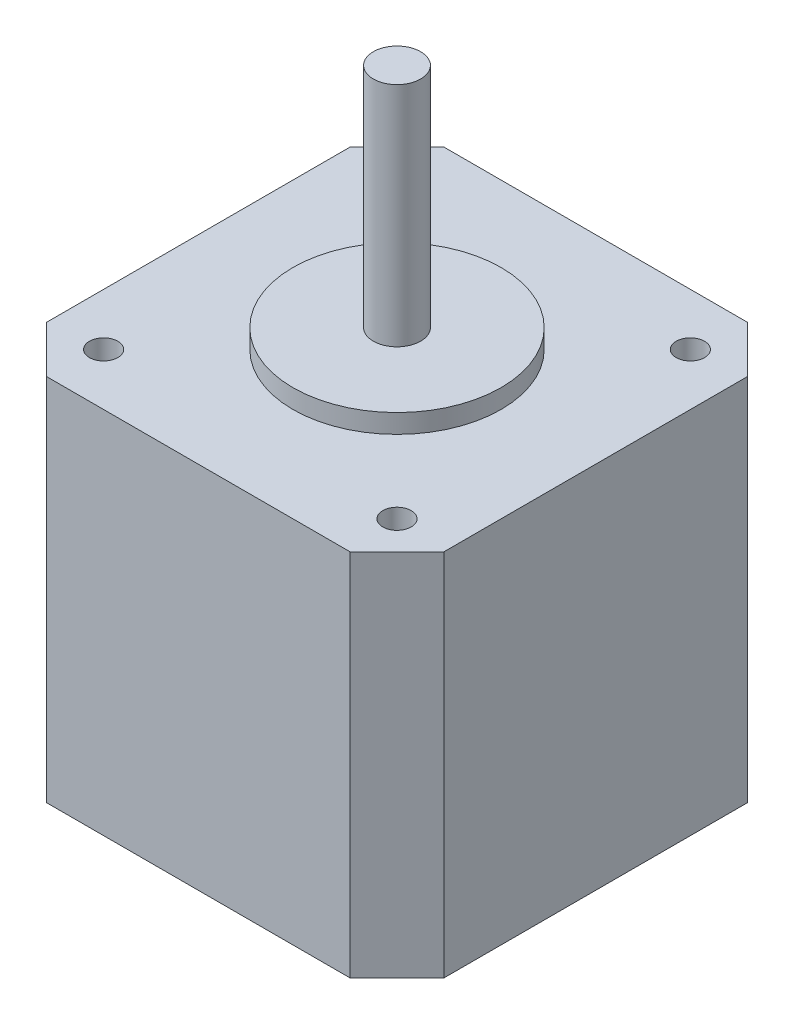
SolidWorks part; units mm, degrees
ref_plane "Front Plane" through (0, 0, 0) normal (0, 0, 1) x (1, 0, 0)
ref_plane "Top Plane" through (0, 0, 0) normal (0, 1, 0) x (1, 0, 0)
ref_plane "Right Plane" through (0, 0, 0) normal (1, 0, 0) x (0, 0, -1)
sketch "Sketch1" plane through (0, 0, 0) normal (0, 1, 0) x (1, 0, 0)
  line L1 (0, 0) -> (42, 0)
  line L2 (0, 0) -> (0, 42)
  line L3 (0, 42) -> (42, 42)
  line L4 (42, 0) -> (42, 42)
  line L5 (0, 0) -> (42, 42) construction
  line L6 (0, 42) -> (42, 0) construction
  point P4 (21, 21)
  dimension "D1" = 42
  dimension "D2" = 42
extrude "Boss-Extrude1" add sketch "Sketch1" along normal blind 39
sketch "Sketch5" plane through (0, 39, 0) normal (0, 1, 0) x (1, 0, 0)
  line L0 (42, 21) -> (0, 21) construction
  line L1 (42, 0) -> (42, 42) construction
  line L2 (0, 42) -> (0, 0) construction
  line L3 (21, 0) -> (21, 42) construction
  line L4 (0, 0) -> (42, 0) construction
  line L5 (42, 42) -> (0, 42) construction
  circle A0 centre (21, 21) radius 11
  dimension "D1" = 22
extrude "Boss-Extrude4" add sketch "Sketch5" along normal blind 2
sketch "Sketch6" plane through (0, 41, 0) normal (0, 1, 0) x (1, 0, 0)
  circle A0 centre (21, 21) radius 2.5
  dimension "D1" = 5
extrude "Boss-Extrude5" add sketch "Sketch6" along normal blind 24
sketch "Sketch8" plane through (0, 39, 0) normal (0, 1, 0) x (1, 0, 0)
  line L0 (36.5, 42) -> (36.5, 0) construction
  line L1 (42, 42) -> (0, 42) construction
  line L2 (0, 0) -> (42, 0) construction
  line L3 (42, 5.5) -> (0, 5.5) construction
  line L4 (42, 0) -> (42, 42) construction
  line L5 (0, 42) -> (0, 0) construction
  line L6 (42, 21) -> (0, 21) construction
  line L7 (21, 42) -> (21, 0) construction
  circle A0 centre (36.5, 5.5) radius 1.5
  circle A1 centre (36.5, 36.5) radius 1.5
  circle A2 centre (5.5, 5.5) radius 1.5
  circle A3 centre (5.5, 36.5) radius 1.5
  dimension "D3" = 3
  dimension "D1" = 15.5
  dimension "D2" = 15.5
extrude "Cut-Extrude1" cut sketch "Sketch8" against normal blind 4.5
sketch "Sketch9" plane through (0, 39, 0) normal (0, 1, 0) x (1, 0, 0)
  line L0 (0, 4.9497) -> (4.9497, 0)
  line L1 (0, 42) -> (0, 0) construction
  line L2 (0, 0) -> (42, 0) construction
  line L3 (37.0503, 0) -> (42, 4.9497)
  line L4 (42, 0) -> (42, 42) construction
  line L5 (37.0503, 42) -> (42, 37.0503)
  line L6 (42, 42) -> (0, 42) construction
  line L7 (0, 37.0503) -> (4.9497, 42)
  line L8 (4.9497, 42) -> (0, 42)
  line L9 (0, 42) -> (0, 37.0503)
  line L10 (0, 4.9497) -> (0, 0)
  line L11 (0, 0) -> (4.9497, 0)
  line L12 (42, 4.9497) -> (42, 0)
  line L13 (42, 0) -> (37.0503, 0)
  line L14 (42, 37.0503) -> (42, 42)
  line L15 (42, 42) -> (37.0503, 42)
  dimension "D1" = 7
  dimension "D2" = 7
  dimension "D3" = 7
  dimension "D4" = 7
extrude "Cut-Extrude2" cut sketch "Sketch9" against normal through all
